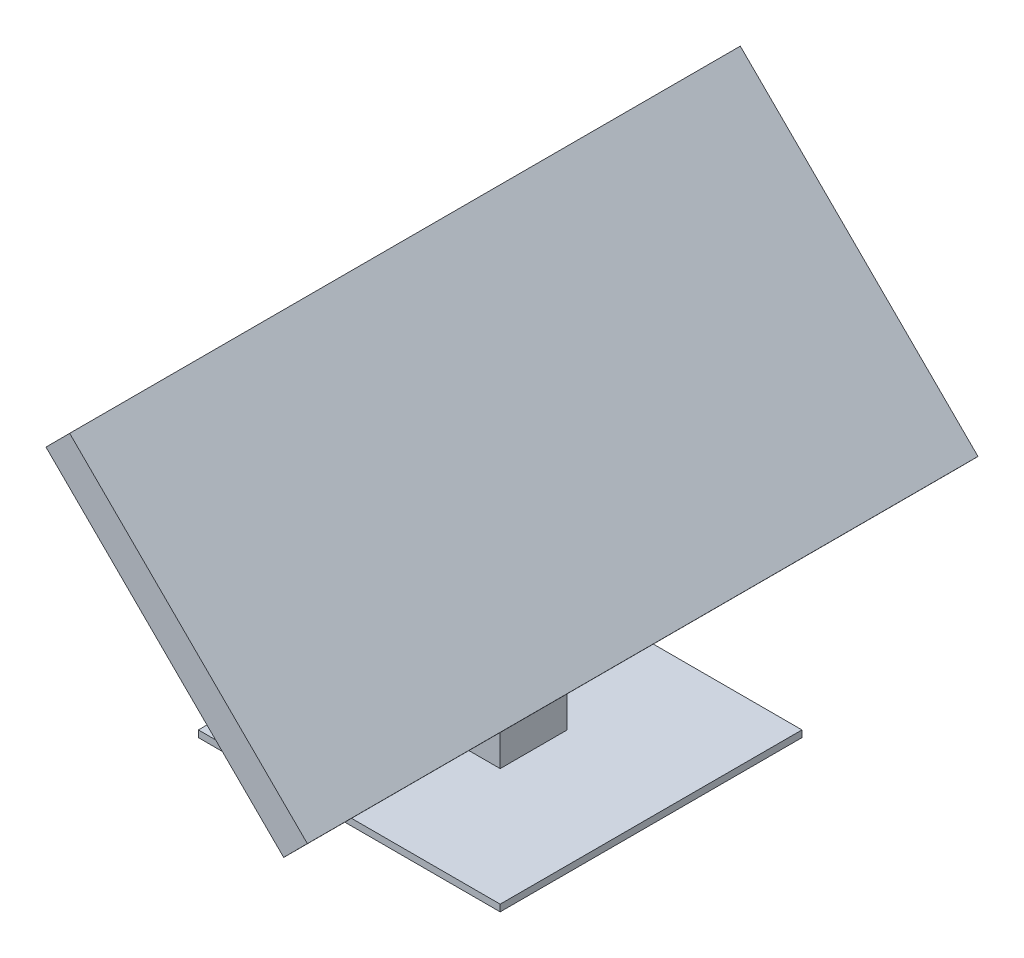
SolidWorks part; units mm, degrees
ref_plane "Front Plane" through (0, 0, 0) normal (0, 0, 1) x (1, 0, 0)
ref_plane "Top Plane" through (0, 0, 0) normal (0, 1, 0) x (1, 0, 0)
ref_plane "Right Plane" through (0, 0, 0) normal (1, 0, 0) x (0, 0, -1)
sketch "Sketch2" plane through (0, 0, 0) normal (0, 1, 0) x (1, 0, 0)
  line L1 (0, 0) -> (45, 0)
  line L2 (0, 0) -> (0, 45)
  line L3 (0, 45) -> (45, 45)
  line L4 (45, 0) -> (45, 45)
  dimension "D1" = 45
  dimension "D2" = 45
extrude "Boss-Extrude1" add sketch "Sketch2" along normal blind 1
sketch "Sketch4" plane through (0, 1, 0) normal (0, 1, 0) x (1, 0, 0)
  line L4 (17.5, 27.5) -> (27.5, 27.5)
  line L5 (17.5, 27.5) -> (17.5, 17.5)
  line L6 (17.5, 17.5) -> (27.5, 17.5)
  line L7 (27.5, 27.5) -> (27.5, 17.5)
  line L8 (17.5, 27.5) -> (27.5, 17.5) construction
  line L9 (17.5, 17.5) -> (27.5, 27.5) construction
  point P4 (22.5, 22.5)
  dimension "D1" = 10
  dimension "D2" = 10
extrude "Boss-Extrude3" add sketch "Sketch4" along normal blind 40 contours L4 L7 L6 L5
ref_plane "Plane1" through (17.5, 41, -17.5) normal (0, 0, 1) x (1, 0, 0)
sketch "Sketch10" plane through (17.5, 41, -17.5) normal (0, 0, 1) x (1, 0, 0)
  line L0 (0, 0) -> (10, -9.9496)
  line L1 (10, 0) -> (10, -40) construction
  line L2 (10, -9.9496) -> (17.9108, -1.9989)
  line L3 (17.9108, -1.9989) -> (8.3582, 7.5056)
  line L4 (8.3582, 7.5056) -> (0, 0)
extrude "Cut-Extrude4" cut sketch "Sketch10" against normal blind 30 contours L0 L2 L3 L4
sketch "Sketch19" plane through (29.2056, 29.3534, 0) normal (0.7053, 0.7089, 0) x (0.7089, -0.7053, 0)
  line L1 (-2.406, 27.5) -> (-16.5126, 27.5)
  line L4 (15.5407, -27.5) -> (-34.4593, -27.5)
  line L5 (15.5407, -27.5) -> (15.5407, 72.5)
  line L6 (15.5407, 72.5) -> (-34.4593, 72.5)
  line L7 (-34.4593, -27.5) -> (-34.4593, 72.5)
  line L8 (15.5407, -27.5) -> (-34.4593, 72.5) construction
  line L9 (15.5407, 72.5) -> (-34.4593, -27.5) construction
  point P4 (-9.4593, 22.5)
  dimension "D1" = 50
  dimension "D2" = 100
extrude "Boss-Extrude10" add sketch "Sketch19" along normal blind 5 contours L4 L7 L6 L5
